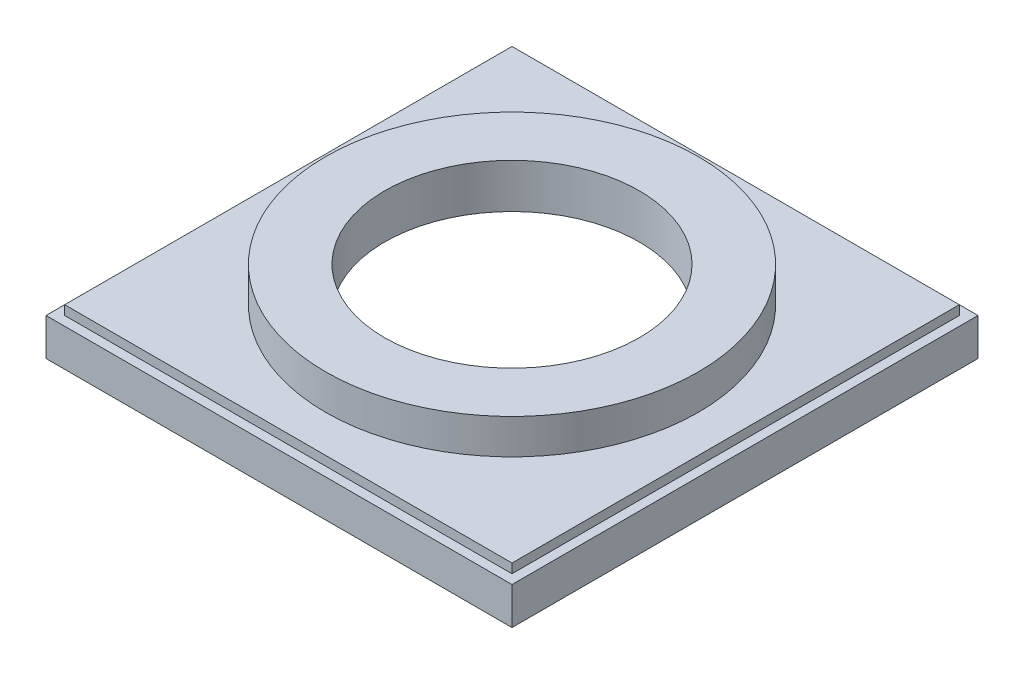
SolidWorks part; units mm, degrees
ref_plane "Front Plane" through (0, 0, 0) normal (0, 0, 1) x (1, 0, 0)
ref_plane "Top Plane" through (0, 0, 0) normal (0, 1, 0) x (1, 0, 0)
ref_plane "Right Plane" through (0, 0, 0) normal (1, 0, 0) x (0, 0, -1)
sketch "Sketch1" plane through (0, 0, 0) normal (0, 1, 0) x (1, 0, 0)
  line L0 (-133.35, 133.35) -> (-133.35, -133.35)
  line L1 (-158.75, 158.75) -> (158.75, 158.75)
  line L2 (-158.75, 158.75) -> (-158.75, -158.75)
  line L3 (-158.75, -158.75) -> (158.75, -158.75)
  line L4 (158.75, 158.75) -> (158.75, -158.75)
  line L5 (-158.75, 158.75) -> (158.75, -158.75) construction
  line L6 (-158.75, -158.75) -> (158.75, 158.75) construction
  line L7 (-133.35, -133.35) -> (133.35, -133.35)
  line L8 (133.35, 133.35) -> (133.35, -133.35)
  line L9 (-133.35, 133.35) -> (133.35, 133.35)
  point P0 (0, 0)
  dimension "D1" = 317.5
  dimension "D2" = 25.4
extrude "Boss-Extrude1" add sketch "Sketch1" along normal blind 25.4
sketch "Sketch2" plane through (0, 25.4, 0) normal (0, 1, 0) x (1, 0, 0)
  line L12 (152.4, -152.4) -> (152.4, 152.4)
  line L13 (152.4, 152.4) -> (-152.4, 152.4)
  line L14 (-152.4, 152.4) -> (-152.4, -152.4)
  line L15 (-152.4, -152.4) -> (152.4, -152.4)
  line L16 (152.4, -152.4) -> (152.4, 152.4)
  line L17 (152.4, 152.4) -> (-152.4, 152.4)
  line L18 (-152.4, 152.4) -> (-152.4, -152.4)
  line L19 (-152.4, -152.4) -> (152.4, -152.4)
  dimension "D1" = 6.35
extrude "Boss-Extrude2" add sketch "Sketch2" along normal blind 6.35
sketch "Sketch3" plane through (0, 31.75, 0) normal (0, 1, 0) x (1, 0, 0)
  circle A0 centre (0, 0) radius 127
  dimension "D1" = 254
extrude "Boss-Extrude3" add sketch "Sketch3" along normal offset from surface (23.876 mm away) 55.626 up to face at (0, 0, 0)
sketch "Sketch4" plane through (0, 55.626, 0) normal (0, 1, 0) x (1, 0, 0)
  circle A0 centre (0, 0) radius 86.741
  dimension "D1" = 173.482
extrude "Cut-Extrude1" cut sketch "Sketch4" against normal through all
